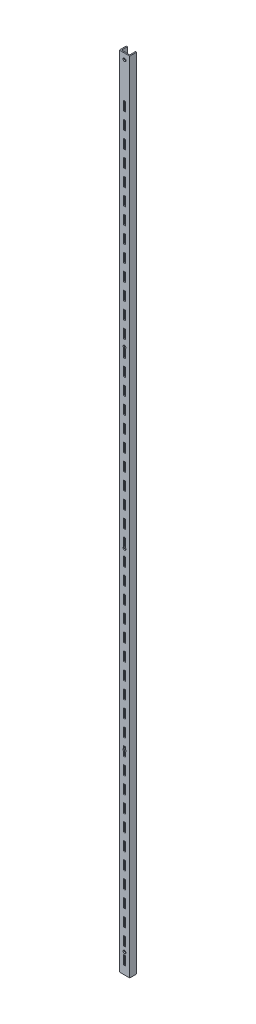
SolidWorks part; units mm, degrees
ref_plane "Front Plane" through (0, 0, 0) normal (0, 0, 1) x (1, 0, 0)
ref_plane "Top Plane" through (0, 0, 0) normal (0, 1, 0) x (1, 0, 0)
ref_plane "Right Plane" through (0, 0, 0) normal (1, 0, 0) x (0, 0, -1)
sketch "Sketch1" plane through (0, 0, 0) normal (0, 1, 0) x (1, 0, 0)
  line L0 (0, 0) -> (0, 10.69)
  line L1 (0, 10.69) -> (1.66, 10.69)
  line L2 (1.66, 10.69) -> (1.66, 1.66)
  line L3 (1.66, 1.66) -> (14.34, 1.66)
  line L4 (14.34, 1.66) -> (14.34, 10.69)
  line L5 (14.34, 10.69) -> (16, 10.69)
  line L6 (16, 10.69) -> (16, 0)
  line L7 (16, 0) -> (0, 0)
  line L8 (8, 1.66) -> (8, 0) construction
  dimension "D1" = 16
  dimension "D2" = 10.69
  dimension "D3" = 1.66
extrude "Boss-Extrude1" add sketch "Sketch1" along normal blind 1219.2
sketch "Sketch2" plane through (0, 0, -1.66) normal (0, 0, -1) x (-1, 0, 0)
  line L0 (-8, 1164.6545) -> (-8, 1127.3259) construction
  line L1 (-9.32, 1155.99) -> (-6.68, 1155.99)
  line L2 (-9.32, 1155.99) -> (-9.32, 1141.99)
  line L3 (-9.32, 1141.99) -> (-6.68, 1141.99)
  line L4 (-6.68, 1155.99) -> (-6.68, 1141.99)
  line L6 (-14.34, 1219.2) -> (-1.66, 1219.2) construction
  line L7 (-9.32, 1130.89) -> (-9.32, 1116.89)
  line L8 (-9.32, 1130.89) -> (-6.68, 1130.89)
  line L9 (-6.68, 1130.89) -> (-6.68, 1116.89)
  line L10 (-9.32, 1116.89) -> (-6.68, 1116.89)
  line L11 (-9.32, 1105.79) -> (-9.32, 1091.79)
  line L12 (-9.32, 1105.79) -> (-6.68, 1105.79)
  line L13 (-6.68, 1105.79) -> (-6.68, 1091.79)
  line L14 (-9.32, 1091.79) -> (-6.68, 1091.79)
  line L15 (-9.32, 1080.69) -> (-9.32, 1066.69)
  line L16 (-9.32, 1080.69) -> (-6.68, 1080.69)
  line L17 (-6.68, 1080.69) -> (-6.68, 1066.69)
  line L18 (-9.32, 1066.69) -> (-6.68, 1066.69)
  line L19 (-9.32, 1055.59) -> (-9.32, 1041.59)
  line L20 (-9.32, 1055.59) -> (-6.68, 1055.59)
  line L21 (-6.68, 1055.59) -> (-6.68, 1041.59)
  line L22 (-9.32, 1041.59) -> (-6.68, 1041.59)
  line L23 (-9.32, 1030.49) -> (-9.32, 1016.49)
  line L24 (-9.32, 1030.49) -> (-6.68, 1030.49)
  line L25 (-6.68, 1030.49) -> (-6.68, 1016.49)
  line L26 (-9.32, 1016.49) -> (-6.68, 1016.49)
  line L27 (-9.32, 1005.39) -> (-9.32, 991.39)
  line L28 (-9.32, 1005.39) -> (-6.68, 1005.39)
  line L29 (-6.68, 1005.39) -> (-6.68, 991.39)
  line L30 (-9.32, 991.39) -> (-6.68, 991.39)
  line L31 (-9.32, 980.29) -> (-9.32, 966.29)
  line L32 (-9.32, 980.29) -> (-6.68, 980.29)
  line L33 (-6.68, 980.29) -> (-6.68, 966.29)
  line L34 (-9.32, 966.29) -> (-6.68, 966.29)
  line L35 (-9.32, 955.19) -> (-9.32, 941.19)
  line L36 (-9.32, 955.19) -> (-6.68, 955.19)
  line L37 (-6.68, 955.19) -> (-6.68, 941.19)
  line L38 (-9.32, 941.19) -> (-6.68, 941.19)
  line L39 (-9.32, 930.09) -> (-9.32, 916.09)
  line L40 (-9.32, 930.09) -> (-6.68, 930.09)
  line L41 (-6.68, 930.09) -> (-6.68, 916.09)
  line L42 (-9.32, 916.09) -> (-6.68, 916.09)
  line L43 (-9.32, 904.99) -> (-9.32, 890.99)
  line L44 (-9.32, 904.99) -> (-6.68, 904.99)
  line L45 (-6.68, 904.99) -> (-6.68, 890.99)
  line L46 (-9.32, 890.99) -> (-6.68, 890.99)
  line L47 (-9.32, 879.89) -> (-9.32, 865.89)
  line L48 (-9.32, 879.89) -> (-6.68, 879.89)
  line L49 (-6.68, 879.89) -> (-6.68, 865.89)
  line L50 (-9.32, 865.89) -> (-6.68, 865.89)
  line L51 (-9.32, 854.79) -> (-9.32, 840.79)
  line L52 (-9.32, 854.79) -> (-6.68, 854.79)
  line L53 (-6.68, 854.79) -> (-6.68, 840.79)
  line L54 (-9.32, 840.79) -> (-6.68, 840.79)
  line L55 (-9.32, 829.69) -> (-9.32, 815.69)
  line L56 (-9.32, 829.69) -> (-6.68, 829.69)
  line L57 (-6.68, 829.69) -> (-6.68, 815.69)
  line L58 (-9.32, 815.69) -> (-6.68, 815.69)
  line L59 (-9.32, 804.59) -> (-9.32, 790.59)
  line L60 (-9.32, 804.59) -> (-6.68, 804.59)
  line L61 (-6.68, 804.59) -> (-6.68, 790.59)
  line L62 (-9.32, 790.59) -> (-6.68, 790.59)
  line L63 (-9.32, 779.49) -> (-9.32, 765.49)
  line L64 (-9.32, 779.49) -> (-6.68, 779.49)
  line L65 (-6.68, 779.49) -> (-6.68, 765.49)
  line L66 (-9.32, 765.49) -> (-6.68, 765.49)
  line L67 (-9.32, 754.39) -> (-9.32, 740.39)
  line L68 (-9.32, 754.39) -> (-6.68, 754.39)
  line L69 (-6.68, 754.39) -> (-6.68, 740.39)
  line L70 (-9.32, 740.39) -> (-6.68, 740.39)
  line L71 (-9.32, 729.29) -> (-9.32, 715.29)
  line L72 (-9.32, 729.29) -> (-6.68, 729.29)
  line L73 (-6.68, 729.29) -> (-6.68, 715.29)
  line L74 (-9.32, 715.29) -> (-6.68, 715.29)
  line L75 (-9.32, 704.19) -> (-9.32, 690.19)
  line L76 (-9.32, 704.19) -> (-6.68, 704.19)
  line L77 (-6.68, 704.19) -> (-6.68, 690.19)
  line L78 (-9.32, 690.19) -> (-6.68, 690.19)
  line L79 (-9.32, 679.09) -> (-9.32, 665.09)
  line L80 (-9.32, 679.09) -> (-6.68, 679.09)
  line L81 (-6.68, 679.09) -> (-6.68, 665.09)
  line L82 (-9.32, 665.09) -> (-6.68, 665.09)
  line L83 (-9.32, 653.99) -> (-9.32, 639.99)
  line L84 (-9.32, 653.99) -> (-6.68, 653.99)
  line L85 (-6.68, 653.99) -> (-6.68, 639.99)
  line L86 (-9.32, 639.99) -> (-6.68, 639.99)
  line L87 (-9.32, 628.89) -> (-9.32, 614.89)
  line L88 (-9.32, 628.89) -> (-6.68, 628.89)
  line L89 (-6.68, 628.89) -> (-6.68, 614.89)
  line L90 (-9.32, 614.89) -> (-6.68, 614.89)
  line L91 (-9.32, 603.79) -> (-9.32, 589.79)
  line L92 (-9.32, 603.79) -> (-6.68, 603.79)
  line L93 (-6.68, 603.79) -> (-6.68, 589.79)
  line L94 (-9.32, 589.79) -> (-6.68, 589.79)
  line L95 (-9.32, 578.69) -> (-9.32, 564.69)
  line L96 (-9.32, 578.69) -> (-6.68, 578.69)
  line L97 (-6.68, 578.69) -> (-6.68, 564.69)
  line L98 (-9.32, 564.69) -> (-6.68, 564.69)
  line L99 (-9.32, 553.59) -> (-9.32, 539.59)
  line L100 (-9.32, 553.59) -> (-6.68, 553.59)
  line L101 (-6.68, 553.59) -> (-6.68, 539.59)
  line L102 (-9.32, 539.59) -> (-6.68, 539.59)
  line L103 (-9.32, 528.49) -> (-9.32, 514.49)
  line L104 (-9.32, 528.49) -> (-6.68, 528.49)
  line L105 (-6.68, 528.49) -> (-6.68, 514.49)
  line L106 (-9.32, 514.49) -> (-6.68, 514.49)
  line L107 (-9.32, 503.39) -> (-9.32, 489.39)
  line L108 (-9.32, 503.39) -> (-6.68, 503.39)
  line L109 (-6.68, 503.39) -> (-6.68, 489.39)
  line L110 (-9.32, 489.39) -> (-6.68, 489.39)
  line L111 (-9.32, 478.29) -> (-9.32, 464.29)
  line L112 (-9.32, 478.29) -> (-6.68, 478.29)
  line L113 (-6.68, 478.29) -> (-6.68, 464.29)
  line L114 (-9.32, 464.29) -> (-6.68, 464.29)
  line L115 (-9.32, 453.19) -> (-9.32, 439.19)
  line L116 (-9.32, 453.19) -> (-6.68, 453.19)
  line L117 (-6.68, 453.19) -> (-6.68, 439.19)
  line L118 (-9.32, 439.19) -> (-6.68, 439.19)
  line L119 (-9.32, 428.09) -> (-9.32, 414.09)
  line L120 (-9.32, 428.09) -> (-6.68, 428.09)
  line L121 (-6.68, 428.09) -> (-6.68, 414.09)
  line L122 (-9.32, 414.09) -> (-6.68, 414.09)
  line L123 (-9.32, 402.99) -> (-9.32, 388.99)
  line L124 (-9.32, 402.99) -> (-6.68, 402.99)
  line L125 (-6.68, 402.99) -> (-6.68, 388.99)
  line L126 (-9.32, 388.99) -> (-6.68, 388.99)
  line L127 (-9.32, 377.89) -> (-9.32, 363.89)
  line L128 (-9.32, 377.89) -> (-6.68, 377.89)
  line L129 (-6.68, 377.89) -> (-6.68, 363.89)
  line L130 (-9.32, 363.89) -> (-6.68, 363.89)
  line L131 (-9.32, 352.79) -> (-9.32, 338.79)
  line L132 (-9.32, 352.79) -> (-6.68, 352.79)
  line L133 (-6.68, 352.79) -> (-6.68, 338.79)
  line L134 (-9.32, 338.79) -> (-6.68, 338.79)
  line L135 (-9.32, 327.69) -> (-9.32, 313.69)
  line L136 (-9.32, 327.69) -> (-6.68, 327.69)
  line L137 (-6.68, 327.69) -> (-6.68, 313.69)
  line L138 (-9.32, 313.69) -> (-6.68, 313.69)
  line L139 (-9.32, 302.59) -> (-9.32, 288.59)
  line L140 (-9.32, 302.59) -> (-6.68, 302.59)
  line L141 (-6.68, 302.59) -> (-6.68, 288.59)
  line L142 (-9.32, 288.59) -> (-6.68, 288.59)
  line L143 (-9.32, 277.49) -> (-9.32, 263.49)
  line L144 (-9.32, 277.49) -> (-6.68, 277.49)
  line L145 (-6.68, 277.49) -> (-6.68, 263.49)
  line L146 (-9.32, 263.49) -> (-6.68, 263.49)
  line L147 (-9.32, 252.39) -> (-9.32, 238.39)
  line L148 (-9.32, 252.39) -> (-6.68, 252.39)
  line L149 (-6.68, 252.39) -> (-6.68, 238.39)
  line L150 (-9.32, 238.39) -> (-6.68, 238.39)
  line L151 (-9.32, 227.29) -> (-9.32, 213.29)
  line L152 (-9.32, 227.29) -> (-6.68, 227.29)
  line L153 (-6.68, 227.29) -> (-6.68, 213.29)
  line L154 (-9.32, 213.29) -> (-6.68, 213.29)
  line L155 (-9.32, 202.19) -> (-9.32, 188.19)
  line L156 (-9.32, 202.19) -> (-6.68, 202.19)
  line L157 (-6.68, 202.19) -> (-6.68, 188.19)
  line L158 (-9.32, 188.19) -> (-6.68, 188.19)
  line L159 (-9.32, 177.09) -> (-9.32, 163.09)
  line L160 (-9.32, 177.09) -> (-6.68, 177.09)
  line L161 (-6.68, 177.09) -> (-6.68, 163.09)
  line L162 (-9.32, 163.09) -> (-6.68, 163.09)
  line L163 (-9.32, 151.99) -> (-9.32, 137.99)
  line L164 (-9.32, 151.99) -> (-6.68, 151.99)
  line L165 (-6.68, 151.99) -> (-6.68, 137.99)
  line L166 (-9.32, 137.99) -> (-6.68, 137.99)
  line L167 (-9.32, 126.89) -> (-9.32, 112.89)
  line L168 (-9.32, 126.89) -> (-6.68, 126.89)
  line L169 (-6.68, 126.89) -> (-6.68, 112.89)
  line L170 (-9.32, 112.89) -> (-6.68, 112.89)
  line L171 (-9.32, 101.79) -> (-9.32, 87.79)
  line L172 (-9.32, 101.79) -> (-6.68, 101.79)
  line L173 (-6.68, 101.79) -> (-6.68, 87.79)
  line L174 (-9.32, 87.79) -> (-6.68, 87.79)
  line L175 (-9.32, 76.69) -> (-9.32, 62.69)
  line L176 (-9.32, 76.69) -> (-6.68, 76.69)
  line L177 (-6.68, 76.69) -> (-6.68, 62.69)
  line L178 (-9.32, 62.69) -> (-6.68, 62.69)
  line L179 (-9.32, 51.59) -> (-9.32, 37.59)
  line L180 (-9.32, 51.59) -> (-6.68, 51.59)
  line L181 (-6.68, 51.59) -> (-6.68, 37.59)
  line L182 (-9.32, 37.59) -> (-6.68, 37.59)
  line L183 (-9.32, 26.49) -> (-9.32, 12.49)
  line L184 (-9.32, 26.49) -> (-6.68, 26.49)
  line L185 (-6.68, 26.49) -> (-6.68, 12.49)
  line L186 (-9.32, 12.49) -> (-6.68, 12.49)
  point P5 (-8, 1155.99)
  point P9 (-8, 1219.2)
  dimension "D1" = 2.64
  dimension "D2" = 63.21
  dimension "D3" = 14
  dimension "D4" = 46
  dimension "D5" = 11.1
extrude "Cut-Extrude1" cut sketch "Sketch2" against normal through all
sketch "Sketch3" plane through (0, 0, -1.66) normal (0, 0, -1) x (-1, 0, 0)
  line L0 (-8, 1225.2426) -> (-8, 1213.1338) construction
  line L2 (-14.34, 1219.2) -> (-1.66, 1219.2) construction
  circle A0 centre (-8, 1210.325) radius 2.195
  circle A1 centre (-8, 830.595) radius 2.195
  circle A2 centre (-8, 563.895) radius 2.195
  circle A3 centre (-8, 297.195) radius 2.195
  circle A4 centre (-8, 30.495) radius 2.195
  point P3 (-8, 1219.1882)
  point P5 (-8, 1219.2)
  dimension "D1" = 4.39
  dimension "D3" = 379.73
  dimension "D4" = 4.39
  dimension "D2" = 8.875
  dimension "D5" = 4
extrude "Cut-Extrude2" cut sketch "Sketch3" against normal through all
